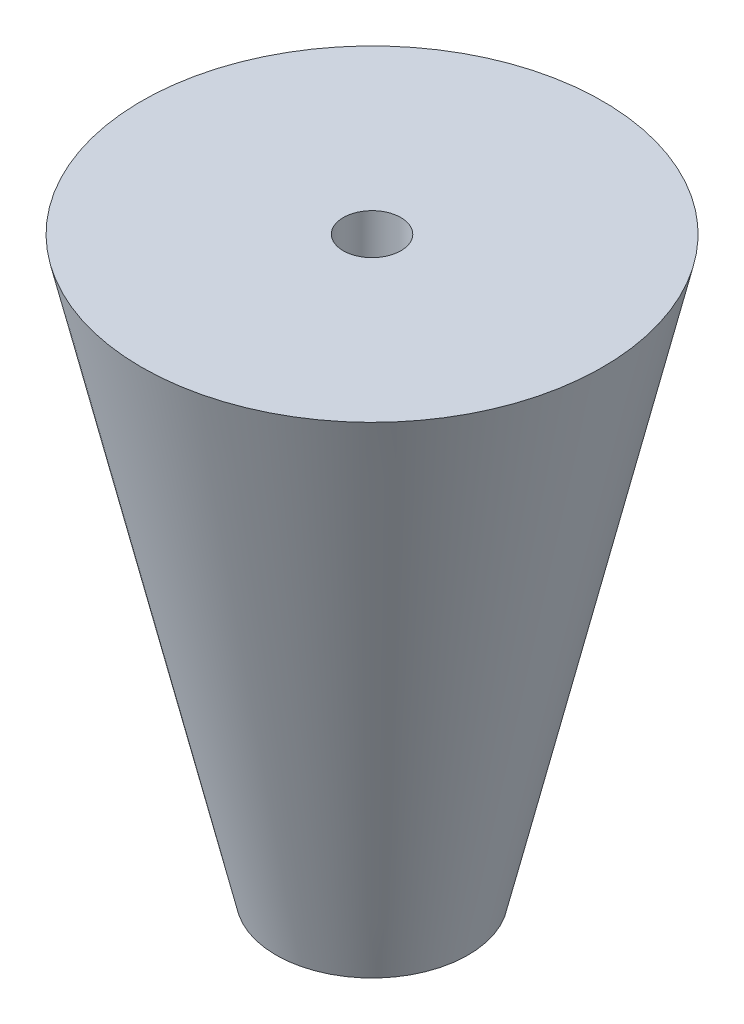
SolidWorks part; units mm, degrees
ref_plane "Front Plane" through (0, 0, 0) normal (0, 0, 1) x (1, 0, 0)
ref_plane "Top Plane" through (0, 0, 0) normal (0, 1, 0) x (1, 0, 0)
ref_plane "Right Plane" through (0, 0, 0) normal (1, 0, 0) x (0, 0, -1)
sketch "Sketch1" plane through (0, 0, 0) normal (0, 0, 1) x (1, 0, 0)
  line L0 (0, 0) -> (0, 30) construction
  line L1 (5, 0) -> (12, 30)
  line L2 (12, 30) -> (0, 30)
  line L3 (0, 30) -> (0, 0)
  line L4 (0, 0) -> (5, 0)
  dimension "D1" = 30
  dimension "D2" = 5
  dimension "D3" = 12
revolve "Revolve1" add sketch "Sketch1" angle 360 about L3
sketch "Sketch2" plane through (0, 30, 0) normal (0, 1, 0) x (1, 0, 0)
  circle A0 centre (0, 0) radius 1.5
  dimension "D1" = 3
extrude "Cut-Extrude1" cut sketch "Sketch2" against normal blind 10
